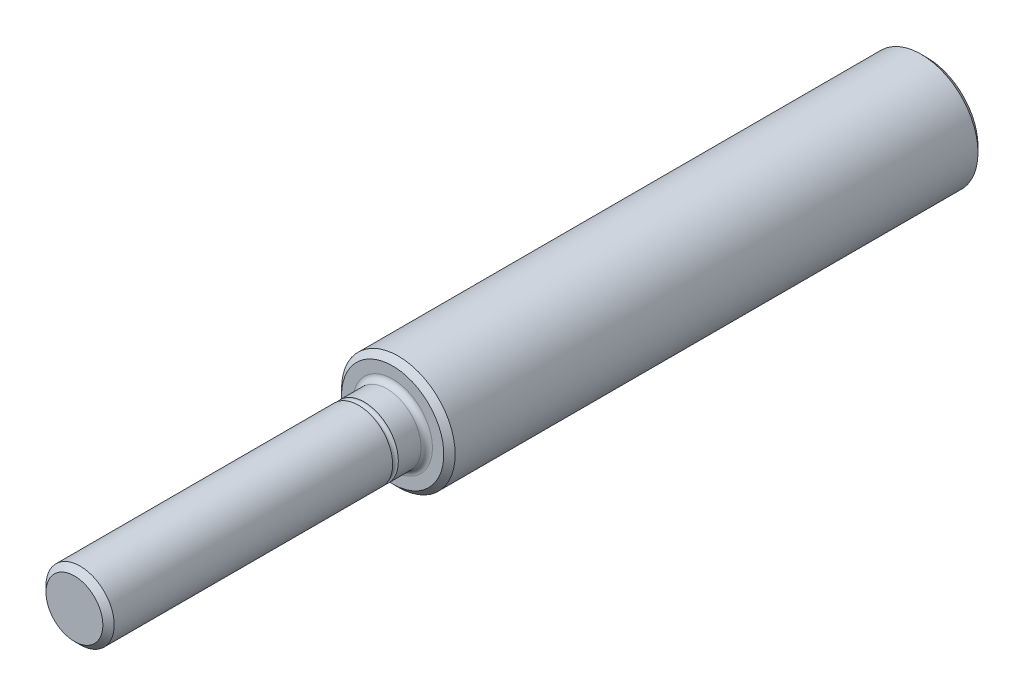
SolidWorks part; units mm, degrees
material "AISI 1020"
ref_plane "Front Plane" through (0, 0, 0) normal (0, 0, 1) x (1, 0, 0)
ref_plane "Top Plane" through (0, 0, 0) normal (0, 1, 0) x (1, 0, 0)
ref_plane "Right Plane" through (0, 0, 0) normal (1, 0, 0) x (0, 0, -1)
sketch "Sketch1" plane through (0, 0, 0) normal (1, 0, 0) x (0, 0, -1)
  line L0 (0, -258.8839) -> (0, 12685.3103) construction
  line L1 (-258.8839, 0) -> (12685.3103, 0) construction
  line L2 (-37.5, 0) -> (37.5, 0)
  line L3 (-9.5, 3) -> (-9.5, 5)
  line L4 (-9.5, 5) -> (37.5, 5)
  line L9 (37.5, 5) -> (37.5, 0)
  line L11 (-37.5, 0) -> (-37.5, 3)
  line L12 (-37.5, 3) -> (-12.5, 3)
  line L13 (-12, 3) -> (-9.5, 3)
  arc A0 (-12.5, 3) -> (-12, 3) centre (-12.25, 3) ccw
  point P7 (0, 0)
  point P10 (-24, 0)
  point P13 (-49.9724, 0)
  dimension "D2" = 0.5
  dimension "D1" = 75
  dimension "D3" = 10
  dimension "D4" = 25.25
  dimension "D5" = 28
  dimension "D6" = 6
revolve "Revolve1" add sketch "Sketch1" angle 360 about L1
cosmetic thread "Cosmetic Thread1" [suppressed] parameters "D1"=15, "D2"=4.891
cosmetic thread "Cosmetic Thread3" parameters "D1"=25, "D2"=4.891
fillet "Fillet1" radius 0.5 1 edges at (3, 0, 9.5)
chamfer "Chamfer1" distance 0.5 angle 45 3 edges at (5, 0, -37.5) (5, 0, 9.5) (3, 0, 37.5)
